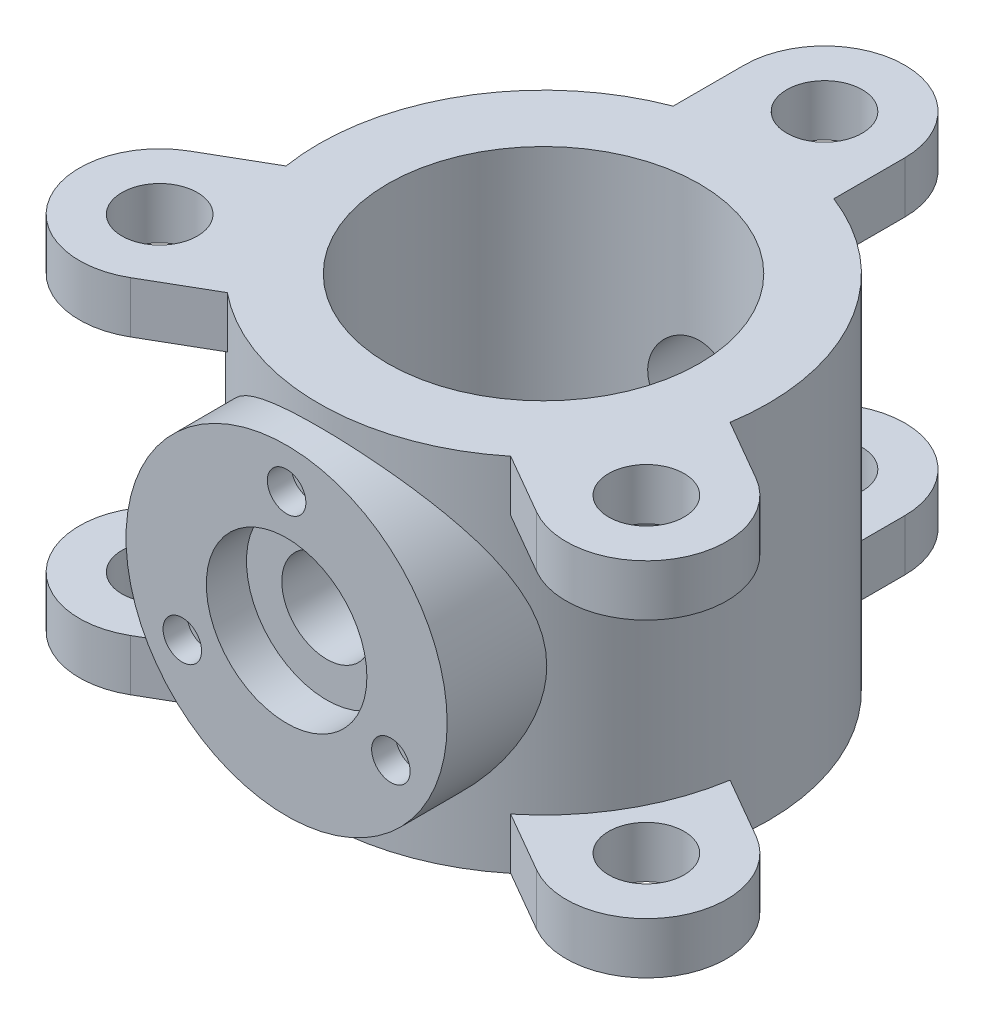
SolidWorks part; units mm, degrees
ref_plane "Front Plane" through (0, 0, 0) normal (0, 0, 1) x (1, 0, 0)
ref_plane "Top Plane" through (0, 0, 0) normal (0, 1, 0) x (1, 0, 0)
ref_plane "Right Plane" through (0, 0, 0) normal (1, 0, 0) x (0, 0, -1)
sketch "Sketch1" plane through (0, 0, 0) normal (0, 1, 0) x (1, 0, 0)
  circle A0 centre (0, 0) radius 97
  circle A1 centre (0, 0) radius 140
  dimension "D1" = 280
  dimension "D2" = 194
extrude "Boss-Extrude1" add sketch "Sketch1" along normal blind 225
sketch "Sketch2" plane through (0, 225, 0) normal (0, 1, 0) x (1, 0, 0)
  line L0 (0, 0) -> (0, 190) construction
  line L1 (-50, 130.767) -> (-50, 175)
  line L2 (50, 175) -> (50, 130.767)
  circle A1 centre (0, 175) radius 23.5
  arc A2 (50, 175) -> (-50, 175) centre (0, 175) ccw
  circle A3 centre (0, 0) radius 140 construction
  arc A5 (50, 130.767) -> (-50, 130.767) centre (0, 0) ccw
  dimension "D1" = 175
  dimension "D3" = 47
  dimension "D4" = 100
  dimension "D2" = 190
extrude "Boss-Extrude2" add sketch "Sketch2" against normal blind 32
pattern_circular "CirPattern1" count 3 over 360 about axis through (0, 0, 0) along (0, 1, 0) of "Boss-Extrude2"
pattern_linear "LPattern2" count 2 spacing 193 along (0, -1, 0) of "Boss-Extrude2"
pattern_circular "CirPattern2" count 3 over 360 about axis through (0, 0, 0) along (0, 1, 0) of "LPattern2"
ref_plane "Plane1" through (0, 0, 160) normal (0, 0, 1) x (1, 0, 0)
sketch "Sketch3" plane through (0, 0, 160) normal (0, 0, 1) x (1, 0, 0)
  circle A0 centre (0, 112.5) radius 100
  point P2 (0, 0)
  dimension "D1" = 200
  dimension "D2" = 112.5
extrude "Boss-Extrude3" add sketch "Sketch3" against normal up to next
sketch "Sketch4" plane through (0, 0, 160) normal (0, 0, 1) x (1, 0, 0)
  circle A0 centre (0, 112.5) radius 28
  dimension "D1" = 56
extrude "Cut-Extrude1" cut sketch "Sketch4" against normal through all
sketch "Sketch5" plane through (0, 0, 160) normal (0, 0, 1) x (1, 0, 0)
  circle A0 centre (0, 112.5) radius 50
  dimension "D1" = 100
extrude "Cut-Extrude2" cut sketch "Sketch5" against normal blind 25
sketch "Sketch6" plane through (0, 0, 160) normal (0, 0, 1) x (1, 0, 0)
  line L0 (0, 112.5) -> (0, 262.0367) construction
  circle A0 centre (0, 187.5) radius 12
  circle A1 centre (64.9519, 75) radius 12
  circle A2 centre (-64.9519, 75) radius 12
  point P12 (0, 112.5)
  dimension "D1" = 24
  dimension "D5" = 64.9519
  dimension "D2" = 75
  dimension "D4" = 64.9519
  dimension "D3" = 3
extrude "Cut-Extrude3" cut sketch "Sketch6" against normal blind 15
